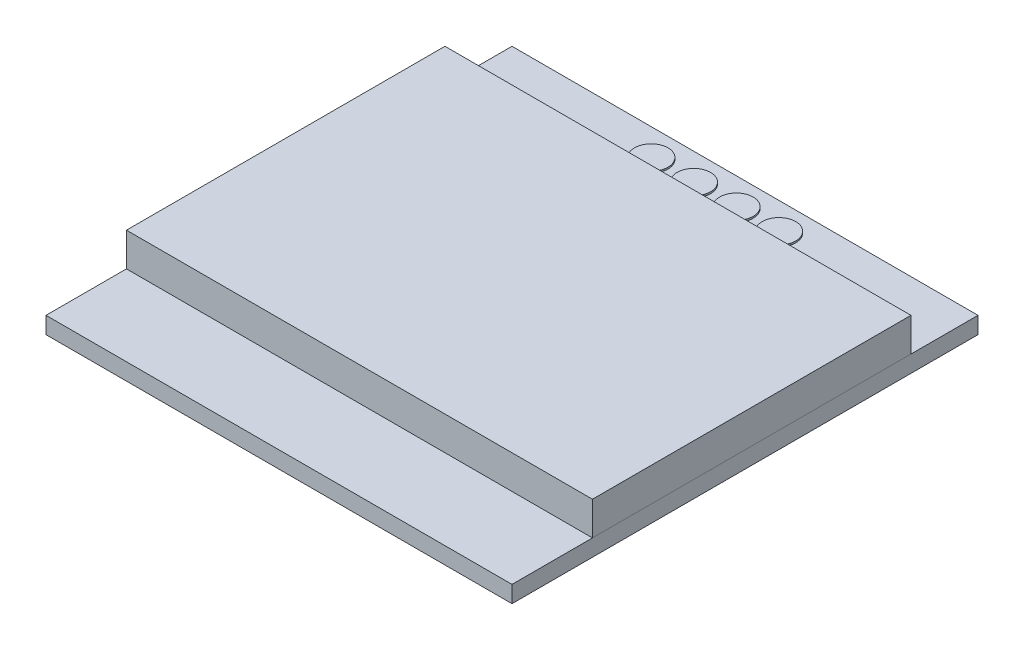
SolidWorks part; units mm, degrees
ref_plane "Спереди" through (0, 0, 0) normal (0, 0, 1) x (1, 0, 0)
ref_plane "Сверху" through (0, 0, 0) normal (0, 1, 0) x (1, 0, 0)
ref_plane "Справа" through (0, 0, 0) normal (1, 0, 0) x (0, 0, -1)
sketch "Sketch1" plane through (0, 0, 0) normal (0, 1, 0) x (1, 0, 0)
  line L1 (0, 0) -> (27.8, 0)
  line L2 (0, 0) -> (0, 27.8)
  line L3 (0, 27.8) -> (27.8, 27.8)
  line L4 (27.8, 0) -> (27.8, 27.8)
  dimension "D1" = 27.8
  dimension "D2" = 27.8
extrude "Boss-Extrude1" add sketch "Sketch1" along normal blind 1
sketch "Sketch2" plane through (0, 1, 0) normal (0, 1, 0) x (1, 0, 0)
  line L0 (0, 27.8) -> (0, 0) construction
  line L1 (0, 23.8) -> (27.8, 23.8)
  line L2 (0, 23.8) -> (0, 4.8)
  line L3 (0, 4.8) -> (27.8, 4.8)
  line L4 (27.8, 23.8) -> (27.8, 4.8)
  line L5 (27.8, 0) -> (27.8, 27.8) construction
  dimension "D1" = 19
  dimension "D2" = 4
extrude "Boss-Extrude2" add sketch "Sketch2" along normal blind 2 separate body
sketch "Sketch3" plane through (0, 1, 0) normal (0, 1, 0) x (1, 0, 0)
  line L0 (0, 27.8) -> (0, 0) construction
  circle A0 centre (10, 26.1069) radius 1
  circle A1 centre (12.54, 26.1069) radius 1
  circle A2 centre (15.08, 26.1069) radius 1
  circle A3 centre (17.62, 26.1069) radius 1
  dimension "D1" = 2.54
  dimension "D2" = 2.54
  dimension "D3" = 2.54
  dimension "D4" = 10
extrude "Boss-Extrude3" add sketch "Sketch3" along normal blind 0.1 separate body
